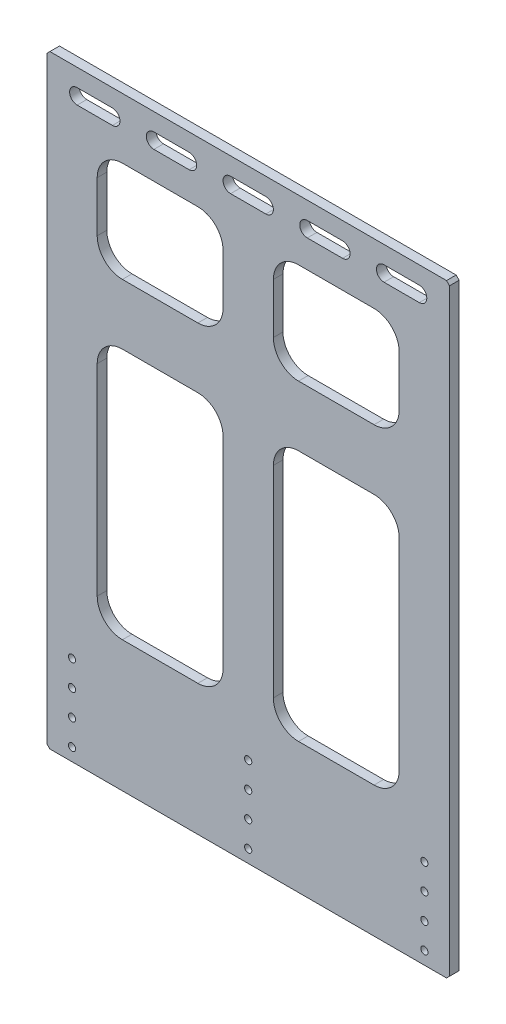
SolidWorks part; units mm, degrees
material "6061-T6 (SS)"
ref_plane "Front Plane" through (0, 0, 0) normal (0, 0, 1) x (1, 0, 0)
ref_plane "Top Plane" through (0, 0, 0) normal (0, 1, 0) x (1, 0, 0)
ref_plane "Right Plane" through (0, 0, 0) normal (1, 0, 0) x (0, 0, -1)
sketch "Sketch1" plane through (0, 0, 0) normal (0, 0, 1) x (1, 0, 0)
  line L0 (-200, 0) -> (200, 0)
  line L1 (-200, 0) -> (-200, 600)
  line L2 (200, 0) -> (200, 600)
  line L3 (-200, 600) -> (200, 600)
  dimension "D1" = 400
  dimension "D2" = 600
extrude "Boss-Extrude1" add sketch "Sketch1" along normal blind 9.525
hole_wizard "1/4 Clearance Hole1" positions "Sketch4" profile "Sketch5" hole size "1/4" standard "ANSI Inch" end condition through all
sketch "Sketch4" plane through (0, 0, 9.525) normal (0, 0, 1) x (1, 0, 0)
  line L0 (-175, 12.7) -> (175, 12.7)
  line L1 (-175, 12.7) -> (-175, 38.1)
  line L2 (175, 12.7) -> (175, 38.1)
  line L3 (-175, 38.1) -> (175, 38.1)
  line L4 (-175, 25.4) -> (175, 25.4) construction
  line L6 (0, 25.4) -> (0, 0) construction
  point P0 (-175, 12.7)
  point P2 (-175, 38.1)
  point P4 (175, 38.1)
  point P6 (175, 12.7)
  point P71 (0, 38.1)
  point P73 (0, 12.7)
  dimension "D1" = 350
  dimension "D2" = 25.4
  dimension "D3" = 25.4
sketch "Sketch5" plane through (-175, 12.7, 9.525) normal (1, 0, 0) x (0, -1, 0)
  line L0 (0, 0) -> (0, 9.525)
  line L1 (0, 9.525) -> (3.5712, 9.525)
  line L2 (3.5712, 9.525) -> (3.5712, 0)
  line L5 (3.5712, 0) -> (0, 0)
  line L11 (0, -6.35) -> (0, 107.95) construction
  dimension "Thru Hole Dia." = 7.1425
  dimension "Thru Hole Depth" = 9.525
pattern_linear "LPattern1" count 2 spacing 50.8 along (0, 1, 0) of "1/4 Clearance Hole1"
sketch "Sketch8" plane through (0, 0, 9.525) normal (0, 0, 1) x (1, 0, 0)
  line L0 (-17.5, 575) -> (17.5, 575) construction
  line L1 (-17.5, 582.5) -> (17.5, 582.5)
  line L2 (-17.5, 567.5) -> (17.5, 567.5)
  line L3 (0, 575) -> (0, 0) construction
  line L4 (200, 600) -> (-200, 600) construction
  arc A0 (-17.5, 582.5) -> (-17.5, 567.5) centre (-17.5, 575) ccw
  arc A1 (17.5, 567.5) -> (17.5, 582.5) centre (17.5, 575) ccw
  point P2 (0, 575)
  dimension "D1" = 15
  dimension "D2" = 35
  dimension "D3" = 25
extrude "Cut-Extrude2" cut sketch "Sketch8" against normal through all
pattern_linear "LPattern2" count 3 spacing 76.2 along (1, 0, 0) count 3 spacing 76.2 along (-1, 0, 0) of "Cut-Extrude2"
sketch "Sketch6" plane through (0, 0, 9.525) normal (0, 0, 1) x (1, 0, 0)
  line L0 (-150, 380) -> (150, 380)
  line L1 (-150, 380) -> (-150, 130)
  line L2 (150, 380) -> (150, 130)
  line L3 (-150, 130) -> (150, 130)
  line L4 (-150, 540) -> (150, 540)
  line L5 (-150, 540) -> (-150, 440)
  line L6 (150, 540) -> (150, 440)
  line L7 (-150, 440) -> (150, 440)
  line L8 (0, 0) -> (0, 130) construction
  line L9 (0, 600) -> (0, 540) construction
  line L10 (200, 600) -> (-200, 600) construction
  line L11 (200, 0) -> (200, 600) construction
  dimension "D1" = 130
  dimension "D2" = 60
  dimension "D3" = 50
  dimension "D4" = 100
  dimension "D5" = 250
extrude "Cut-Extrude1" cut sketch "Sketch6" against normal through all
sketch "Sketch7" plane through (0, 0, 9.525) normal (0, 0, 1) x (1, 0, 0)
  line L0 (-25, 540) -> (-25, 130)
  line L1 (-25, 540) -> (25, 540)
  line L2 (-25, 130) -> (25, 130)
  line L3 (25, 540) -> (25, 130)
  line L4 (150, 540) -> (-150, 540) construction
  line L5 (-150, 130) -> (150, 130) construction
  line L6 (0, 130) -> (0, 0) construction
  dimension "D1" = 50
extrude "Boss-Extrude2" add sketch "Sketch7" against normal through all
fillet "Fillet1" radius 25 16 edges at (-150, 130, 4.7625) (-150, 380, 4.7625) (150, 380, 4.7625) (150, 130, 4.7625) (150, 440, 4.7625) (150, 540, 4.7625) (-150, 440, 4.7625) (-150, 540, 4.7625) (25, 130, 4.7625) (25, 380, 4.7625) (-25, 380, 4.7625) (-25, 440, 4.7625) (25, 440, 4.7625) (25, 540, 4.7625) (-25, 540, 4.7625) (-25, 130, 4.7625)
chamfer "Chamfer2" distance 3 angle 45 4 edges at (200, 0, 4.7625) (-200, 0, 4.7625) (200, 600, 4.7625) (-200, 600, 4.7625)
